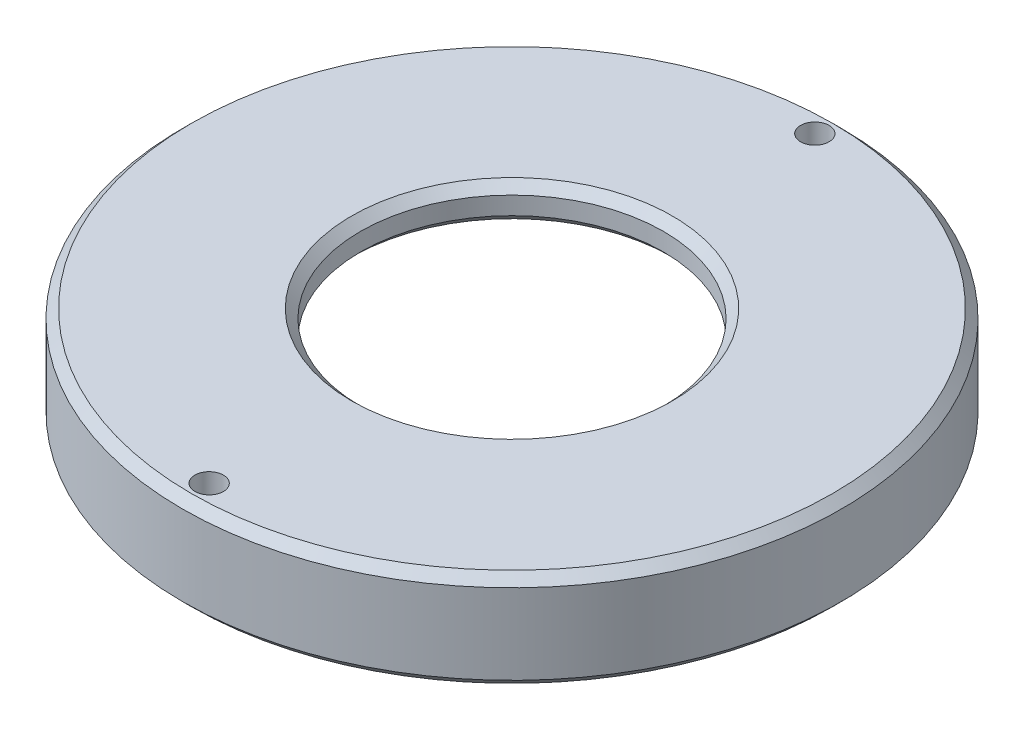
SolidWorks part; units mm, degrees
material "AISI 1020"
ref_plane "Front Plane" through (0, 0, 0) normal (0, 0, 1) x (1, 0, 0)
ref_plane "Top Plane" through (0, 0, 0) normal (0, 1, 0) x (1, 0, 0)
ref_plane "Right Plane" through (0, 0, 0) normal (1, 0, 0) x (0, 0, -1)
sketch "Sketch2" plane through (0, 0, 0) normal (0, 0, 1) x (1, 0, 0)
  line L0 (0, 0) -> (0, 31.4556) construction
  line L1 (15.5, 0) -> (15.5, -3.5)
  line L2 (8.5, 0) -> (15.5, 0)
  line L3 (8.5, 0) -> (8.5, 2)
  line L4 (8.5, 2) -> (18.5, 2)
  line L5 (15.5, -3.5) -> (18.5, -3.5)
  line L6 (18.5, -3.5) -> (18.5, 2)
  dimension "D1" = 2
  dimension "D2" = 3
  dimension "D3" = 8.5
  dimension "D5" = 15.5
  dimension "D8" = 3.5
revolve "Revolve1" add sketch "Sketch2" angle 360 about L0
chamfer "Chamfer1" distance 0.5 angle 45 6 edges at (0, -3.5, -18.5) (0, 2, -8.5) (0, 0, -8.5) (0, 0, -15.5) (0, 2, -18.5) (0, -3.5, -15.5)
hole_wizard "M2x0.4 Tapped Hole1" positions "3DSketch1" profile "Sketch3" tap size "M2x0.4" standard "Ansi Metric"
sketch3d "3DSketch1"
  line L0 (0, 0, 0) -> (0, -3.5, 0) construction
  point P0 (0, -3.5, 17)
  point P2 (0, -3.5, -17)
  dimension "D1" = 17
  dimension "D2" = 17
sketch "Sketch3" plane through (0, -3.5, 17) normal (1, 0, 0) x (0, 0, -1)
  line L0 (0, 0) -> (0, 15.6807)
  line L1 (0, 15.6807) -> (0.8, 15.2)
  line L2 (0.8, 15.2) -> (0.8, 0)
  line L5 (0.8, 0) -> (0, 0)
  line L10 (0, 15.6807) -> (-0.8, 15.2) construction
  line L11 (0, -6.35) -> (0, 107.95) construction
  dimension "Tap Drill Dia." = 1.6
  dimension "Tap Drill Depth" = 15.2
  dimension "Drill Angle" = 118
cosmetic thread "Hole Thread1"
cosmetic thread "Hole Thread2"
